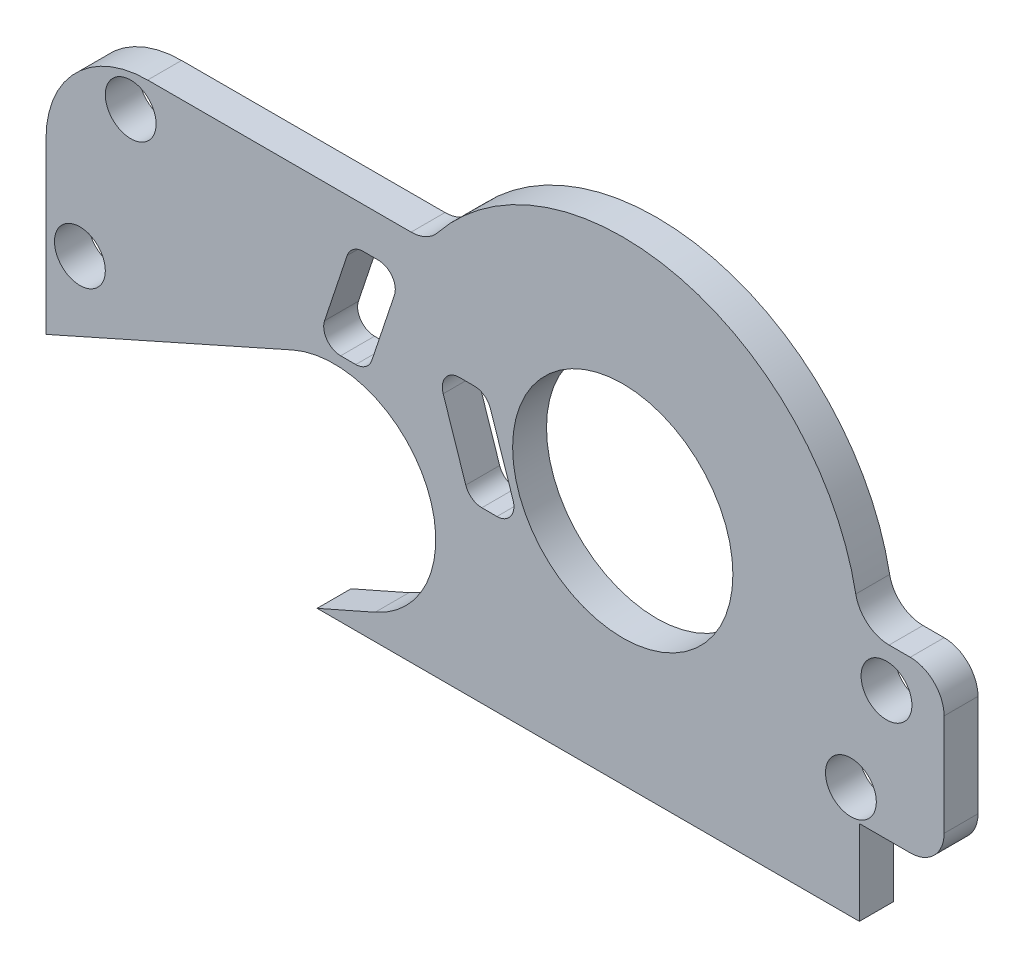
SolidWorks part; units mm, degrees
ref_plane "Front Plane" through (0, 0, 0) normal (0, 0, 1) x (1, 0, 0)
ref_plane "Top Plane" through (0, 0, 0) normal (0, 1, 0) x (1, 0, 0)
ref_plane "Right Plane" through (0, 0, 0) normal (1, 0, 0) x (0, 0, -1)
sketch "Sketch1" plane through (0, 0, 0) normal (0, 0, 1) x (1, 0, 0)
  line L0 (-17.0179, -7) -> (6.9821, -7)
  line L1 (-17.0179, -7) -> (-17.0179, 1)
  line L2 (-14.0179, 4) -> (-6.245, 4)
  line L3 (6.9821, -7) -> (6.9821, -5.5)
  line L4 (7.9821, -4.5) -> (8.4821, -4.5)
  line L5 (9.4821, -3.5) -> (9.4821, -0.5)
  line L6 (8.4821, 0.5) -> (7.8581, 0.5)
  line L7 (6.9821, -5.5) -> (6.9821, -4.5)
  line L8 (6.9821, -4.5) -> (7.9821, -4.5)
  arc A0 (-14.0179, 4) -> (-17.0179, 1) centre (-14.0179, 1) ccw
  arc A1 (6.8759, 1.3125) -> (-5.4644, 4.375) centre (0, 0) ccw
  arc A2 (9.4821, -0.5) -> (8.4821, 0.5) centre (8.4821, -0.5) ccw
  arc A3 (8.4821, -4.5) -> (9.4821, -3.5) centre (8.4821, -3.5) ccw
  arc A5 (-6.245, 4) -> (-5.4644, 4.375) centre (-6.245, 5) ccw
  arc A6 (6.8759, 1.3125) -> (7.8581, 0.5) centre (7.8581, 1.5) ccw
  point P8 (-17.0179, 4)
  point P15 (9.4821, 0.5)
  point P18 (9.4821, -4.5)
  point P21 (6.9821, -4.5)
  point P26 (6.9821, 0.5)
  dimension "D4" = 3
  dimension "D5" = 14
  dimension "D10" = 1
  dimension "D1" = 7
  dimension "D2" = 24
  dimension "D3" = 11
  dimension "D6" = 2.5
  dimension "D7" = 2.5
  dimension "D8" = 5
  dimension "D9" = 2.5
extrude "Boss-Extrude1" add sketch "Sketch1" along normal blind 1
sketch "Sketch3" plane through (0, 0, 1) normal (0, 0, 1) x (1, 0, 0)
  line L0 (-8.3242, -0.2) -> (-7.8783, -0.2)
  line L1 (-8.7985, 0.4581) -> (-8.1318, 2.4581)
  line L2 (-7.4039, 0.1419) -> (-6.7373, 2.1419)
  line L3 (-7.6575, 2.8) -> (-7.2116, 2.8)
  line L4 (-4.8242, 1) -> (-4.3783, 1)
  line L5 (-5.2985, 0.3419) -> (-4.6318, -1.6581)
  line L6 (-3.9039, 0.6581) -> (-3.2373, -1.3419)
  line L7 (-4.1575, -2) -> (-3.7116, -2)
  line L8 (9.4821, -3.5) -> (9.4821, -0.5) construction
  line L10 (-17.0179, -7) -> (6.9821, -7) construction
  line L11 (-6.245, 4) -> (-14.0179, 4) construction
  line L13 (-17.0179, 1) -> (-17.0179, -7) construction
  line L14 (-17.0179, -4) -> (-9.7379, -0.7593)
  line L15 (-9.0179, -7) -> (-7.3064, -6.2445)
  circle A0 centre (0, 0) radius 3.25
  arc A1 (-4.6318, -1.6581) -> (-4.1575, -2) centre (-4.1575, -1.5) ccw
  arc A2 (-3.2373, -1.3419) -> (-3.7116, -2) centre (-3.7116, -1.5) cw
  arc A3 (-4.3783, 1) -> (-3.9039, 0.6581) centre (-4.3783, 0.5) cw
  arc A4 (-5.2985, 0.3419) -> (-4.8242, 1) centre (-4.8242, 0.5) cw
  arc A5 (-8.7985, 0.4581) -> (-8.3242, -0.2) centre (-8.3242, 0.3) ccw
  arc A6 (-7.8783, -0.2) -> (-7.4039, 0.1419) centre (-7.8783, 0.3) ccw
  arc A7 (-6.7373, 2.1419) -> (-7.2116, 2.8) centre (-7.2116, 2.3) ccw
  arc A8 (-8.1318, 2.4581) -> (-7.6575, 2.8) centre (-7.6575, 2.3) cw
  arc A9 (-7.3064, -6.2445) -> (-9.7379, -0.7593) centre (-8.5179, -3.5) ccw
  point P26 (-3.0179, -2)
  point P29 (-4.0179, 1)
  point P32 (-5.5179, 1)
  point P35 (-9.0179, -0.2)
  point P42 (-8.0179, 2.8)
  line M11 (-17.0179, 1) -> (-17.0179, -7)
  line M12 (-17.0179, -7) -> (6.9821, -7)
  dimension "D1" = 6.5
  dimension "D10" = 0.5
  dimension "D11" = 6
  dimension "D2" = 13.5
  dimension "D3" = 12.5
  dimension "D4" = 5
  dimension "D5" = 3
  dimension "D6" = 1.5
  dimension "D7" = 1.2
  dimension "D8" = 9
  dimension "D9" = 8
  dimension "D12" = 8.5
  dimension "D13" = 3.5
  dimension "D14" = 3
  dimension "D15" = 8
extrude "Cut-Extrude2" cut sketch "Sketch3" against normal blind 10 contours L15 A9 L14 M11 M12 | A8 L1 A5 L0 A6 L2 A7 L3 | A4 L5 A1 L7 A2 L6 A3 L4 | A0
sketch "Sketch4" plane through (0, 0, 1) normal (0, 0, 1) x (1, 0, 0)
  line L0 (-9.0179, -7) -> (6.9821, -7) construction
  line L2 (-17.0179, 1) -> (-17.0179, -4) construction
  line L3 (-6.245, 4) -> (-14.0179, 4) construction
  line L4 (9.4821, -3.5) -> (9.4821, -0.5) construction
  line L5 (8.4821, 0.5) -> (7.8581, 0.5) construction
  circle A0 centre (-14.5179, 3) radius 0.75
  circle A1 centre (-16.0179, -1.5) radius 0.75
  circle A2 centre (7.7821, -0.7) radius 0.75
  circle A3 centre (6.7321, -3.7) radius 0.75
  dimension "D1" = 1.5
  dimension "D2" = 5.5
  dimension "D3" = 1
  dimension "D4" = 1
  dimension "D5" = 3.3
  dimension "D6" = 2.75
  dimension "D7" = 1.7
  dimension "D8" = 1.2
  dimension "D9" = 2.5
extrude "Cut-Extrude3" cut sketch "Sketch4" against normal blind 10
sketch "Sketch5" plane through (0, 0, 0) normal (0, 0, -1) x (-1, 0, 0)
  line L0 (3.9039, 0.6581) -> (3.2373, -1.3419) construction
  line L1 (5.2985, 0.3419) -> (4.6318, -1.6581) construction
  line L2 (5.2985, 0.3419) -> (4.6318, -1.6581) construction
  circle A0 centre (4.2152, -0.6581) radius 0.7115
  point P11 (4.9652, -0.6581)
